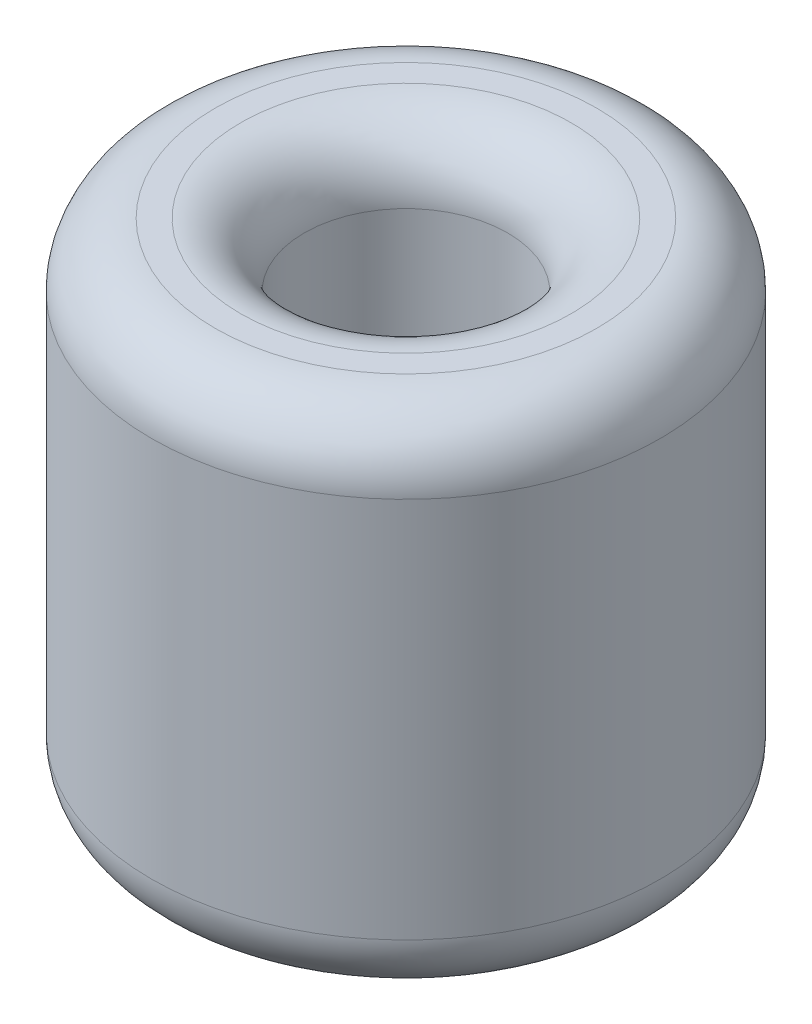
SolidWorks part; units mm, degrees
ref_plane "Front Plane" through (0, 0, 0) normal (0, 0, 1) x (1, 0, 0)
ref_plane "Top Plane" through (0, 0, 0) normal (0, 1, 0) x (1, 0, 0)
ref_plane "Right Plane" through (0, 0, 0) normal (1, 0, 0) x (0, 0, -1)
sketch "Sketch1" plane through (0, 0, 0) normal (0, 1, 0) x (1, 0, 0)
  circle A0 centre (0, 0) radius 1.6
  circle A1 centre (0, 0) radius 4
  dimension "D1" = 3.2
  dimension "D2" = 8
extrude "Boss-Extrude1" add sketch "Sketch1" along normal blind 8
fillet "Fillet1" radius 1 3 edges at (0, 0, 4) (0, 8, 4) (0, 8, 1.6)
